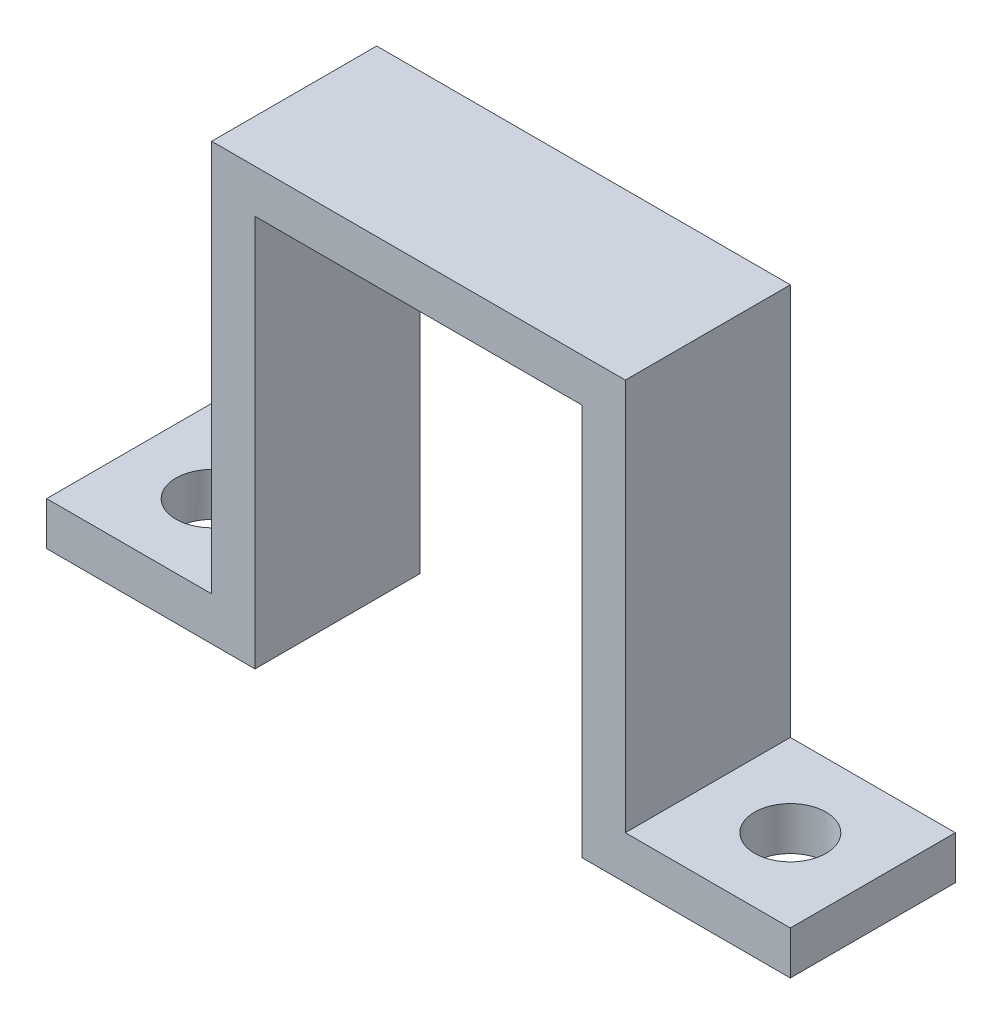
SolidWorks part; units mm, degrees
ref_plane "Front Plane" through (0, 0, 0) normal (0, 0, 1) x (1, 0, 0)
ref_plane "Top Plane" through (0, 0, 0) normal (0, 1, 0) x (1, 0, 0)
ref_plane "Right Plane" through (0, 0, 0) normal (1, 0, 0) x (0, 0, -1)
sketch "Sketch1" plane through (0, 0, 0) normal (0, 0, 1) x (1, 0, 0)
  line L0 (9.55, 0) -> (-9.55, 0)
  line L1 (-9.55, 0) -> (-9.55, -18.1)
  line L2 (-9.55, -18.1) -> (-17.17, -18.1)
  line L3 (-17.17, -18.1) -> (-17.17, -20.1)
  line L4 (-17.17, -20.1) -> (-7.55, -20.1)
  line L5 (-7.55, -20.1) -> (-7.55, -2)
  line L6 (-7.55, -2) -> (7.55, -2)
  line L7 (0, -2) -> (0, 0) construction
  line L8 (7.55, -20.1) -> (7.55, -2)
  line L9 (17.17, -20.1) -> (7.55, -20.1)
  line L10 (17.17, -18.1) -> (17.17, -20.1)
  line L11 (9.55, -18.1) -> (17.17, -18.1)
  line L12 (9.55, 0) -> (9.55, -18.1)
  dimension "D1" = 2
  dimension "D2" = 2
  dimension "D3" = 2
  dimension "D4" = 7.62
  dimension "D5" = 18.1
  dimension "D6" = 7.55
extrude "Boss-Extrude1" add sketch "Sketch1" along normal mid plane 7.62
sketch "Sketch2" plane through (0, -18.1, 0) normal (0, 1, 0) x (1, 0, 0)
  line L0 (-9.55, 3.81) -> (-17.17, 3.81) construction
  circle A0 centre (-13.36, 0) radius 1.65
  point P4 (-13.36, 3.81)
  dimension "D1" = 3.3
extrude "Cut-Extrude1" cut sketch "Sketch2" against normal up to surface (2 mm away) up to face at (-12.36, -20.1, 0)
mirror "Mirror1" about plane through (0, 0, 0) normal (1, 0, 0) of "Cut-Extrude1"
